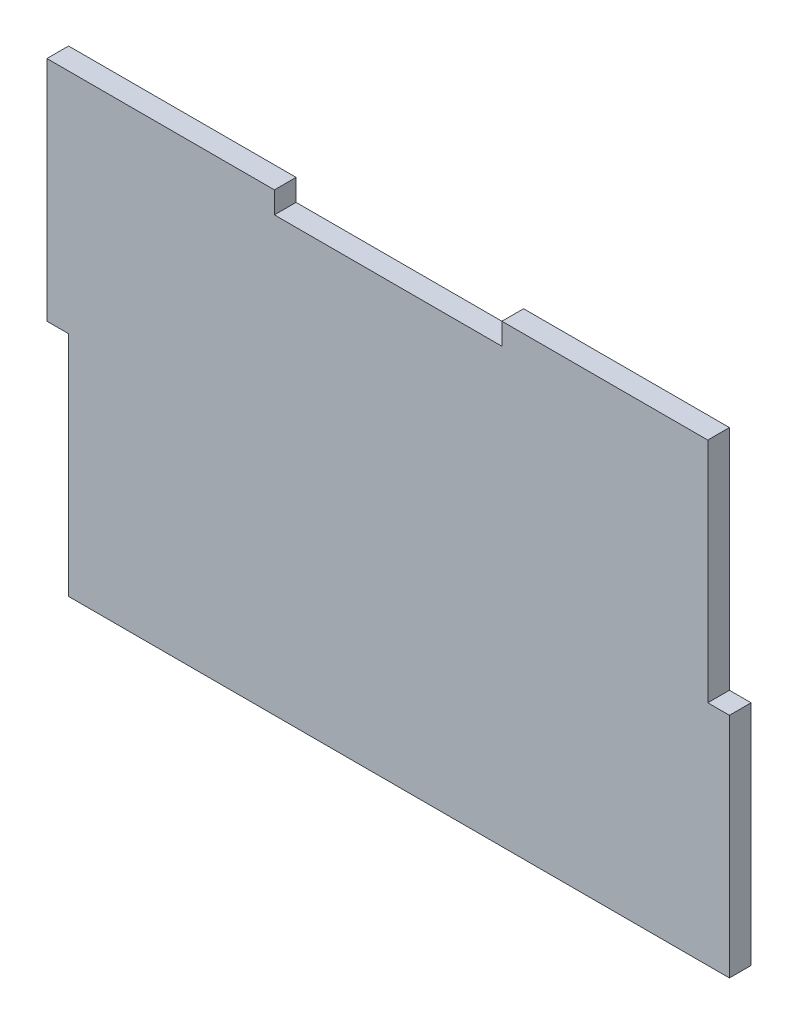
SolidWorks part; units mm, degrees
ref_plane "Front Plane" through (0, 0, 0) normal (0, 0, 1) x (1, 0, 0)
ref_plane "Top Plane" through (0, 0, 0) normal (0, 1, 0) x (1, 0, 0)
ref_plane "Right Plane" through (0, 0, 0) normal (1, 0, 0) x (0, 0, -1)
sketch "Sketch1" plane through (0, 0, 0) normal (0, 0, 1) x (1, 0, 0)
  line L0 (-50, 16.6667) -> (-50, 50)
  line L1 (46.825, -50) -> (-50, -50) construction
  line L2 (50, -16.6667) -> (50, 16.6667)
  line L3 (46.825, 50) -> (16.6667, 50)
  line L4 (-50, -50) -> (-50, -16.6667) construction
  line L5 (50, -50) -> (-50, 50) construction
  line L6 (50, 50) -> (-50, -50) construction
  line L8 (-16.6667, 50) -> (-16.6667, 46.825)
  line L9 (-16.6667, 46.825) -> (16.6667, 46.825)
  line L10 (16.6667, 50) -> (16.6667, 46.825)
  line L11 (-50, 16.6667) -> (-46.825, 16.6667)
  line L13 (-50, -16.6667) -> (-46.825, -16.6667) construction
  line L14 (-46.825, 16.6667) -> (-46.825, -16.6667)
  line L15 (50, 16.6667) -> (46.825, 16.6667)
  line L18 (46.825, 16.6667) -> (46.825, 50)
  line L21 (50, -16.6667) -> (46.825, -16.6667)
  line L22 (46.825, -50) -> (46.825, -16.6667) construction
  line L23 (-16.6667, 50) -> (-50, 50)
  line L24 (-46.825, -16.6667) -> (46.825, -16.6667)
  point P0 (0, 0)
  dimension "D1" = 100
  dimension "D2" = 100
  dimension "D3" = 33.3333
  dimension "D4" = 33.3333
  dimension "D5" = 33.3333
  dimension "D6" = 33.3333
  dimension "D7" = 33.3333
  dimension "D8" = 33.3333
  dimension "D10" = 3.175
  dimension "D11" = 3.175
  dimension "D12" = 3.175
  dimension "D9" = 3.175
extrude "Boss-Extrude1" add sketch "Sketch1" along normal blind 3.175
equation "\"BoxLength\"=10"
equation "\"D1@Sketch1\"=\"BoxLength\""
equation "\"D2@Sketch1\"=\"BoxLength\""
